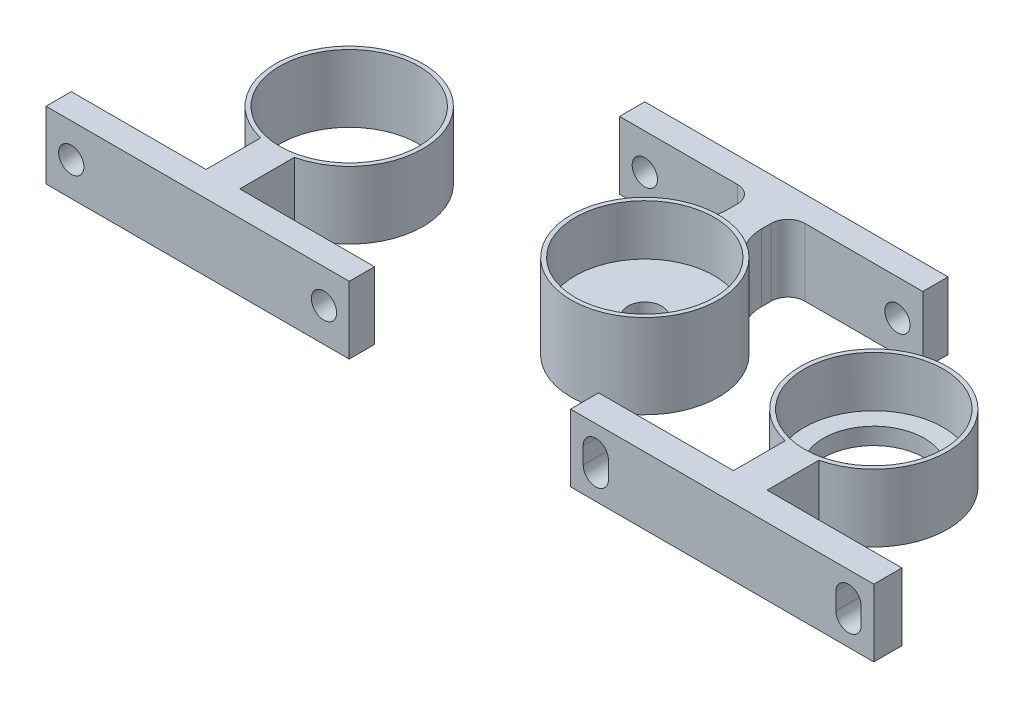
SolidWorks part; units mm, degrees
ref_plane "前视基准面" through (0, 0, 0) normal (0, 0, 1) x (1, 0, 0)
ref_plane "上视基准面" through (0, 0, 0) normal (0, 1, 0) x (1, 0, 0)
ref_plane "右视基准面" through (0, 0, 0) normal (1, 0, 0) x (0, 0, -1)
sketch "草图1" plane through (0, 0, 0) normal (0, 1, 0) x (1, 0, 0)
  circle A0 centre (0, 0) radius 8.25
  circle A1 centre (0, 0) radius 8.75
  dimension "D1" = 16.5
  dimension "D2" = 17.5
extrude "凸台-拉伸2" add sketch "草图1" along normal blind 10
sketch "草图2" plane through (0, 0, 0) normal (0, 1, 0) x (1, 0, 0)
  circle A0 centre (0, 0) radius 8.25
  circle A1 centre (0, 0) radius 2
  dimension "D1" = 4
extrude "凸台-拉伸3" add sketch "草图2" along normal blind 4
sketch "草图3" plane through (0, 0, 0) normal (0, 1, 0) x (1, 0, 0)
  line L0 (-2, 8.5184) -> (2, 8.5184)
  line L1 (-15, 18) -> (-15, 15)
  line L2 (2, 18) -> (15, 18)
  line L3 (-2, 8.5184) -> (-2, 15)
  line L4 (2, 8.5184) -> (2, 15)
  line L5 (-15, 18) -> (-2, 18)
  line L6 (-15, 15) -> (-2, 15)
  line L7 (15, 15) -> (15, 18)
  line L8 (2, 15) -> (15, 15)
  line L9 (2, 18) -> (-2, 18)
  circle A2 centre (0, 0) radius 8.75 construction
  dimension "D1" = 13
  dimension "D2" = 13
  dimension "D3" = 3
  dimension "D4" = 3
extrude "凸台-拉伸4" add sketch "草图3" along normal blind 8
sketch "草图5" plane through (15, 0, 0) normal (1, 0, 0) x (0, 0, -1)
  line L0 (15, 8) -> (18, 8)
  line L1 (15, 8) -> (15, 0)
  line L2 (18, 8) -> (18, 0)
  line L3 (15, 0) -> (18, 0)
  dimension "D1" = 8
extrude "凸台-拉伸5" add sketch "草图5" along normal blind 3
sketch "草图6" plane through (-15, 0, 0) normal (-1, 0, 0) x (0, 0, 1)
  line L0 (-18, 8) -> (-15, 8)
  line L1 (-18, 8) -> (-18, 0)
  line L2 (-15, 8) -> (-15, 0)
  line L3 (-18, 0) -> (-15, 0)
  dimension "D1" = 8
extrude "凸台-拉伸6" add sketch "草图6" along normal blind 3
sketch "草图7" plane through (0, 0, -18) normal (0, 0, -1) x (-1, 0, 0)
  circle A0 centre (-15, 3.754) radius 1.5
  dimension "D2" = 3
extrude "切除-拉伸1" cut sketch "草图7" against normal blind 3
mirror "镜向1" about plane through (0, 0, 0) normal (1, 0, 0) of "切除-拉伸1"
fillet "圆角1" radius 5 2 edges at (2, 4, -8.5184) (-2, 4, -8.5184)
fillet "圆角3" radius 2 2 edges at (-2, 4, -15) (2, 4, -15)
ref_plane "基准面1" through (0, 0, 10) normal (0, 0, 1) x (1, 0, 0)
sketch "草图8" plane through (0, 0, 0) normal (0, 1, 0) x (1, 0, 0)
  circle A0 centre (27.185, 0) radius 8.75
  circle A1 centre (27.185, 0) radius 8.25
  dimension "D1" = 17.5
  dimension "D2" = 16.5
extrude "凸台-拉伸7" add sketch "草图8" along normal blind 8 separate body
sketch "草图9" plane through (0, 0, 0) normal (0, -1, 0) x (1, 0, 0)
  circle A0 centre (27.185, 0) radius 8.25
  circle A1 centre (27.185, 0) radius 6
  dimension "D1" = 12
extrude "凸台-拉伸8" add sketch "草图9" against normal blind 2
sketch "草图10" plane through (0, 0, 0) normal (0, 1, 0) x (1, 0, 0)
  line L1 (27.185, -18) -> (45.185, -18)
  line L2 (27.185, -18) -> (9.185, -18)
  line L3 (9.185, -18) -> (9.185, -14.6639)
  line L4 (9.185, -14.6639) -> (25.185, -14.6639)
  line L5 (45.185, -18) -> (45.185, -14.6639)
  line L6 (45.185, -14.6639) -> (29.185, -14.6639)
  line L7 (25.185, -14.6639) -> (25.185, -8.5184)
  line L8 (25.185, -8.5184) -> (29.185, -8.5184)
  line L9 (29.185, -8.5184) -> (29.185, -14.6639)
  circle A0 centre (27.185, 0) radius 8.75 construction
  dimension "D2" = 18
  dimension "D3" = 18
  dimension "D4" = 16
  dimension "D5" = 16
extrude "凸台-拉伸9" add sketch "草图10" along normal blind 8
sketch "草图11" plane through (0, 0, 18) normal (0, 0, 1) x (1, 0, 0)
  circle A0 centre (12.185, 4) radius 1.5
  circle A1 centre (42.185, 4) radius 1.5
  dimension "D3" = 3
  dimension "D4" = 3
  dimension "D2" = 30
extrude "切除-拉伸2" cut sketch "草图11" against normal blind 8
sketch "草图12" plane through (0, 0, 18) normal (0, 0, 1) x (1, 0, 0)
  line L0 (10.685, 4) -> (10.685, 5)
  line L1 (13.685, 4) -> (13.685, 5)
  line L2 (10.685, 4) -> (10.685, 3)
  line L3 (13.685, 4) -> (13.685, 3)
  circle A0 centre (12.185, 4) radius 1.5 construction
  arc A1 (13.685, 5) -> (10.685, 5) centre (12.185, 5) ccw
  arc A2 (10.685, 3) -> (13.685, 3) centre (12.185, 3) ccw
  dimension "D1" = 1
  dimension "D2" = 1
  dimension "D3" = 1
  dimension "D4" = 1
extrude "切除-拉伸3" cut sketch "草图12" against normal blind 8
sketch "草图13" plane through (0, 0, 18) normal (0, 0, 1) x (1, 0, 0)
  line L0 (40.685, 4) -> (40.685, 5)
  line L2 (43.685, 5) -> (43.685, 4)
  line L3 (43.685, 4) -> (43.685, 3)
  line L5 (40.685, 3) -> (40.685, 4)
  circle A0 centre (42.185, 4) radius 1.5 construction
  arc A1 (43.685, 5) -> (40.685, 5) centre (42.185, 5) ccw
  arc A2 (40.685, 3) -> (43.685, 3) centre (42.185, 3) ccw
  dimension "D1" = 1
  dimension "D2" = 1
  dimension "D3" = 1
extrude "切除-拉伸4" cut sketch "草图13" against normal blind 8
sketch "草图14" plane through (0, 0, 0) normal (0, 1, 0) x (1, 0, 0)
  circle A0 centre (-35.0916, 0) radius 8.75
  circle A1 centre (-35.0916, 0) radius 8.25
  dimension "D1" = 17.5
  dimension "D2" = 16.5
extrude "凸台-拉伸10" add sketch "草图14" along normal blind 8 separate body
sketch "草图15" plane through (0, 0, 0) normal (0, 1, 0) x (1, 0, 0)
  line L0 (-37.0916, -15) -> (-37.0916, -8.5184)
  line L2 (-17.0916, -18) -> (-53.0916, -18)
  line L3 (-53.0916, -18) -> (-53.0916, -15)
  line L4 (-53.0916, -15) -> (-37.0916, -15)
  line L5 (-37.0916, -8.5184) -> (-33.0916, -8.5184)
  line L6 (-33.0916, -15) -> (-17.0916, -15)
  line L7 (-17.0916, -15) -> (-17.0916, -18)
  line L8 (-33.0916, -8.5184) -> (-33.0916, -15)
  circle A0 centre (-35.0916, 0) radius 8.75 construction
  dimension "D4" = 3
  dimension "D5" = 16
  dimension "D6" = 16
extrude "凸台-拉伸11" add sketch "草图15" along normal blind 8
sketch "草图16" plane through (0, 0, 18) normal (0, 0, 1) x (1, 0, 0)
  circle A0 centre (-50.0916, 4) radius 1.5
  circle A1 centre (-20.0916, 4) radius 1.5
  dimension "D3" = 3
  dimension "D4" = 3
extrude "切除-拉伸5" cut sketch "草图16" against normal blind 8
